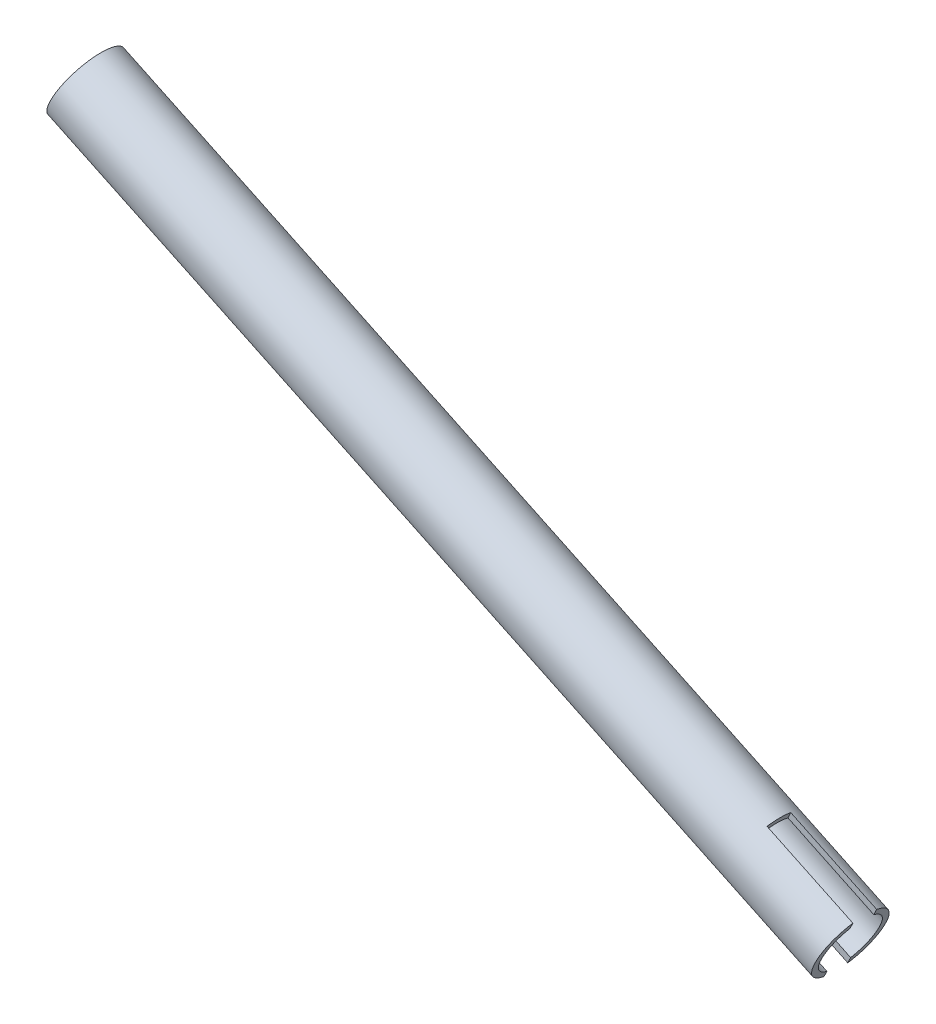
SolidWorks part; units mm, degrees
ref_plane "Front" through (0, 0, 0) normal (0, 0, 1) x (1, 0, 0)
ref_plane "Top" through (0, 0, 0) normal (0, 1, 0) x (1, 0, 0)
ref_plane "Right" through (0, 0, 0) normal (1, 0, 0) x (0, 0, -1)
sketch "Sketch1" plane through (0, 0, 0) normal (0, 0, 1) x (1, 0, 0)
  line L0 (319.8799, -1443.5581) -> (524.0316, -1540.7729) construction
  line L1 (275.4478, -1422.4) -> (581.3633, -1568.0737) construction
  line L2 (524.0316, -1540.7729) -> (520.6463, -1547.8821) construction
  line L3 (520.6463, -1547.8821) -> (519.9365, -1549.3727)
  line L4 (519.9365, -1549.3727) -> (315.7847, -1452.1578)
  line L5 (315.7847, -1452.1578) -> (316.4946, -1450.6672)
  line L6 (316.4946, -1450.6672) -> (520.6463, -1547.8821)
  line L7 (319.8799, -1443.5581) -> (316.4946, -1450.6672) construction
  dimension "D1" = 1.651
  dimension "D2" = 9.525
revolve "Revolve1" add sketch "Sketch1" angle 360 about L0
sketch "Sketch2" plane through (1025.2495, -488.2128, 0) normal (0.9029, -0.4299, 0) x (0, 0, -1)
  line L0 (-3.175, -1180.616) -> (-3.175, -1174.8828) construction
  line L1 (-3.175, -1156.2804) -> (3.175, -1156.2804)
  line L2 (-3.175, -1156.2804) -> (-3.175, -1175.3304)
  line L3 (-3.175, -1175.3304) -> (3.175, -1175.3304)
  line L4 (3.175, -1156.2804) -> (3.175, -1175.3304)
  line L5 (3.175, -1186.0761) -> (3.175, -1180.616) construction
  circle A0 centre (0, -1165.8054) radius 9.525 construction
  point P4 (0, -1175.3304)
  point P7 (0, -1156.2804)
extrude "Cut-Extrude1" cut sketch "Sketch2" against normal up to surface (25.4 mm away)
equation "\"D1@Sketch1\"=\"a arm tube thickness@FS2-SU-FS-A-0002-V1, FRONT LEFT SUSPENSION.SLDASM\""
equation "\"D2@Sketch1\"=\"a arm tube diameter@FS2-SU-FS-A-0002-V1, FRONT LEFT SUSPENSION.SLDASM\"/2"
